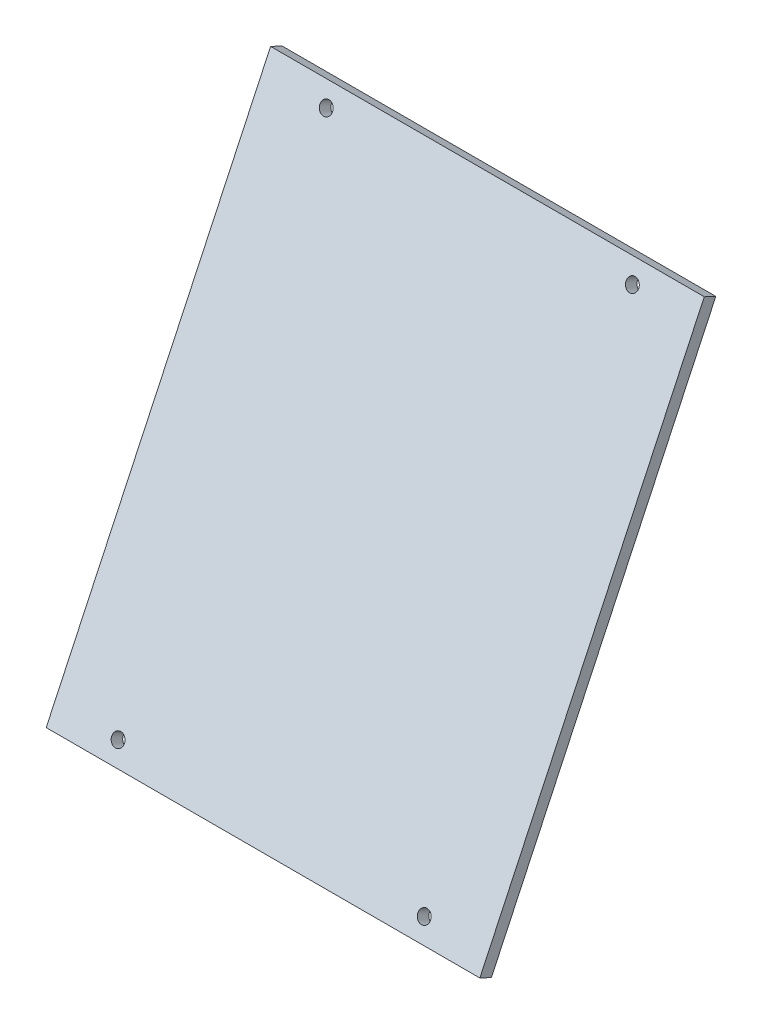
SolidWorks part; units mm, degrees
material "PC High Viscosity"
ref_plane "Front Plane" through (0, 0, 0) normal (0, 0, 1) x (1, 0, 0)
ref_plane "Top Plane" through (0, 0, 0) normal (0, 1, 0) x (1, 0, 0)
ref_plane "Right Plane" through (0, 0, 0) normal (1, 0, 0) x (0, 0, -1)
sketch "Sketch1" plane through (0, 0, 0) normal (1, 0, 0) x (0, 0, -1)
  line L0 (0, 0) -> (111.7276, 237.8381)
  line L1 (111.7276, 237.8381) -> (105.9802, 240.538)
  line L2 (105.9802, 240.538) -> (-5.7474, 2.6999)
  line L3 (-5.7474, 2.6999) -> (0, 0)
  dimension "D1" = 240.538
  dimension "D2" = 117.475
  dimension "D3" = 6.35
extrude "Boss-Extrude1" add sketch "Sketch1" along normal blind 215.9
hole_wizard "1/4 (0.25) Diameter Hole1" positions "Sketch2" profile "Sketch3" hole size "1/4" standard "ANSI Inch" end condition through all
sketch "Sketch2" plane through (0, 2.6999, 5.7474) normal (0, 0.4252, 0.9051) x (1, 0, 0)
  line L0 (0, 262.7737) -> (0, 0) construction
  line L1 (215.9, 262.7737) -> (0, 262.7737) construction
  line L2 (0, 131.3868) -> (215.9, 131.3868) construction
  line L3 (215.9, 262.7737) -> (215.9, 0) construction
  line L4 (107.95, 262.7737) -> (107.95, 0) construction
  line L5 (215.9, 0) -> (0, 0) construction
  point P0 (31.75, 253.2487)
  point P2 (184.15, 253.2487)
  point P18 (184.15, 9.525)
  point P19 (31.75, 9.525)
  point P25 (0, 0)
  point P26 (184.15, 253.2487)
  dimension "D1" = 31.75
  dimension "D3" = 9.525
sketch "Sketch3" plane through (31.75, 231.9169, -101.9303) normal (1, 0, 0) x (0, -0.9051, 0.4252)
  line L0 (0, 0) -> (0, 107.4753)
  line L1 (0, 107.4753) -> (3.175, 107.4753)
  line L2 (3.175, 107.4753) -> (3.175, 0)
  line L5 (3.175, 0) -> (0, 0)
  line L11 (0, -6.35) -> (0, 107.95) construction
  dimension "Thru Hole Dia." = 6.35
  dimension "Thru Hole Depth" = 107.4753
